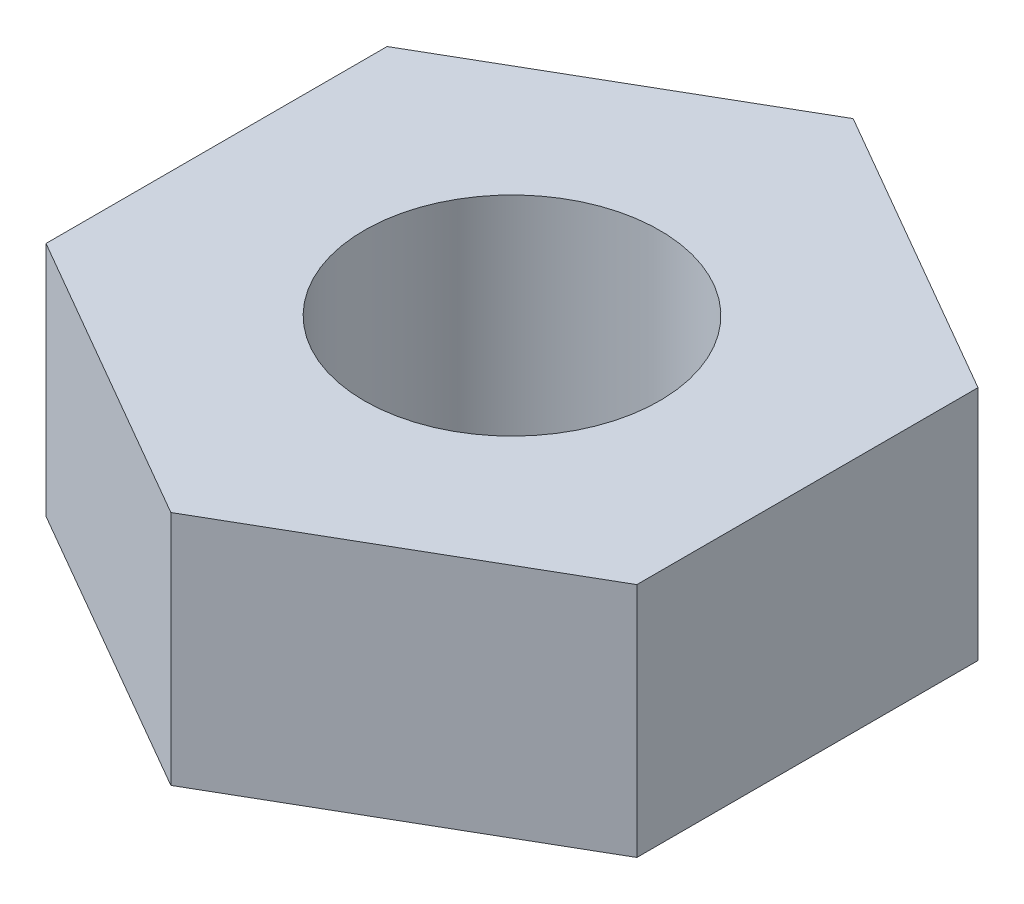
SolidWorks part; units mm, degrees
ref_plane "Front Plane" through (0, 0, 0) normal (0, 0, 1) x (1, 0, 0)
ref_plane "Top Plane" through (0, 0, 0) normal (0, 1, 0) x (1, 0, 0)
ref_plane "Right Plane" through (0, 0, 0) normal (1, 0, 0) x (0, 0, -1)
sketch "Sketch1" plane through (0, 0, 0) normal (0, 1, 0) x (1, 0, 0)
  line L1 (2, -1.1547) -> (2, 1.1547)
  line L2 (2, 1.1547) -> (0, 2.3094)
  line L3 (0, 2.3094) -> (-2, 1.1547)
  line L4 (-2, 1.1547) -> (-2, -1.1547)
  line L5 (-2, -1.1547) -> (0, -2.3094)
  line L6 (0, -2.3094) -> (2, -1.1547)
  circle A0 centre (0, 0) radius 2 construction
  circle A1 centre (0, 0) radius 1
  point P1 (-2, 0)
  dimension "D2" = 2
  dimension "D1" = 4
extrude "Boss-Extrude1" add sketch "Sketch1" along normal blind 1.6
